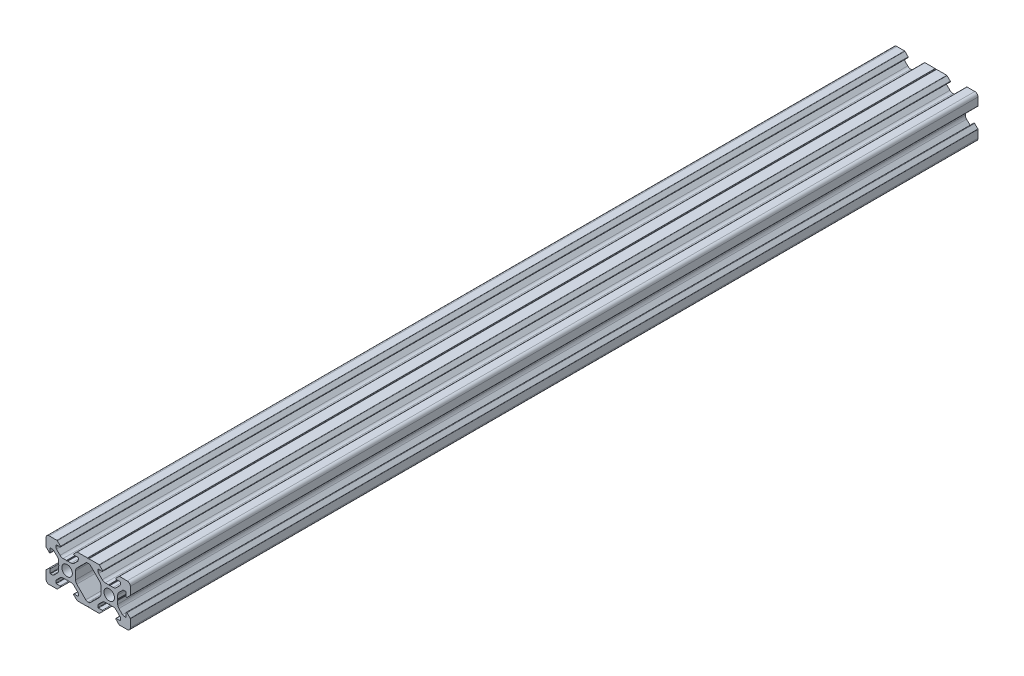
SolidWorks part; units mm, degrees
material "6063-T5"
ref_plane "Спереди" through (0, 0, 0) normal (0, 0, 1) x (1, 0, 0)
ref_plane "Сверху" through (0, 0, 0) normal (0, 1, 0) x (1, 0, 0)
ref_plane "Справа" through (0, 0, 0) normal (1, 0, 0) x (0, 0, -1)
sketch "Model" plane through (0, 0, 0) normal (0, 0, 1) x (1, 0, 0)
  line L0 (-5.4142, 2.9753) -> (-1.1373, 7.2523)
  line L1 (-6, -2.2365) -> (-6, 1.5611)
  line L2 (-5.4142, -3.6507) -> (-1.1373, -7.9276)
  line L3 (-0.1473, -8.3377) -> (0.1473, -8.3377)
  line L4 (5.4142, -3.6507) -> (1.1373, -7.9276)
  line L5 (6, -2.2365) -> (6, 1.5611)
  line L6 (5.4142, 2.9753) -> (1.1373, 7.2523)
  line L7 (-0.1473, 7.6623) -> (0.1473, 7.6623)
  line L8 (0.3757, 9.6623) -> (5.17, 9.6623)
  line L9 (5.3468, 9.5891) -> (6.8468, 8.0891)
  line L10 (6.67, 7.6623) -> (4.9, 7.6623)
  line L11 (4.7, 7.4623) -> (4.7, 6.6493)
  line L12 (4.9929, 5.9422) -> (6.687, 4.2481)
  line L13 (8.1012, 3.6623) -> (9.6623, 3.6623)
  line L14 (9.8185, 3.6075) -> (10, 3.4623)
  line L15 (10.1815, 3.6075) -> (10, 3.4623)
  line L16 (13.313, 4.2481) -> (15.0071, 5.9422)
  line L17 (15.3, 6.6493) -> (15.3, 7.4623)
  line L18 (15.1, 7.6623) -> (13.33, 7.6623)
  line L19 (14.6532, 9.5891) -> (13.1532, 8.0891)
  line L20 (14.83, 9.6623) -> (18.5, 9.6623)
  line L21 (20, 4.4923) -> (20, 8.1623)
  line L22 (19.9268, 4.3155) -> (18.4268, 2.8155)
  line L23 (18, 4.7623) -> (18, 2.9923)
  line L24 (16.987, 4.9623) -> (17.8, 4.9623)
  line L25 (14.5858, 2.9753) -> (16.2799, 4.6694)
  line L26 (14, 0) -> (14, 1.5611)
  line L27 (13.9452, -0.1562) -> (13.8, -0.3377)
  line L28 (13.9452, -0.5192) -> (13.8, -0.3377)
  line L29 (14, -0.6754) -> (14, -2.2365)
  line L30 (14.5858, -3.6507) -> (16.2799, -5.3448)
  line L31 (16.987, -5.6377) -> (17.8, -5.6377)
  line L32 (18, -5.4377) -> (18, -3.6677)
  line L33 (19.9268, -4.9909) -> (18.4268, -3.4909)
  line L34 (20, -5.1677) -> (20, -8.8377)
  line L35 (14.83, -10.3377) -> (18.5, -10.3377)
  line L36 (14.6532, -10.2645) -> (13.1532, -8.7645)
  line L37 (15.1, -8.3377) -> (13.33, -8.3377)
  line L38 (15.3, -7.3247) -> (15.3, -8.1377)
  line L39 (13.313, -4.9235) -> (15.0071, -6.6176)
  line L40 (10.3377, -4.3377) -> (11.8988, -4.3377)
  line L41 (10.1815, -4.2829) -> (10, -4.1377)
  line L42 (9.8185, -4.2829) -> (10, -4.1377)
  line L43 (8.1012, -4.3377) -> (9.6623, -4.3377)
  line L44 (4.9929, -6.6176) -> (6.687, -4.9235)
  line L45 (4.7, -8.1377) -> (4.7, -7.3247)
  line L46 (6.67, -8.3377) -> (4.9, -8.3377)
  line L47 (5.3468, -10.2645) -> (6.8468, -8.7645)
  line L48 (0.3757, -10.3377) -> (5.17, -10.3377)
  line L49 (0, -10.1377) -> (0.237, -10.2957)
  line L50 (0, -10.1377) -> (-0.237, -10.2957)
  line L51 (-0.3757, -10.3377) -> (-5.17, -10.3377)
  line L52 (-5.3468, -10.2645) -> (-6.8468, -8.7645)
  line L53 (-6.67, -8.3377) -> (-4.9, -8.3377)
  line L54 (-4.7, -8.1377) -> (-4.7, -7.3247)
  line L55 (-4.9929, -6.6176) -> (-6.687, -4.9235)
  line L56 (-8.1012, -4.3377) -> (-9.6623, -4.3377)
  line L57 (-9.8185, -4.2829) -> (-10, -4.1377)
  line L58 (-10.1815, -4.2829) -> (-10, -4.1377)
  line L59 (-10.3377, -4.3377) -> (-11.8988, -4.3377)
  line L60 (-13.313, -4.9235) -> (-15.0071, -6.6176)
  line L61 (-15.3, -7.3247) -> (-15.3, -8.1377)
  line L62 (-15.1, -8.3377) -> (-13.33, -8.3377)
  line L63 (-14.6532, -10.2645) -> (-13.1532, -8.7645)
  line L64 (-14.83, -10.3377) -> (-18.5, -10.3377)
  line L65 (-20, -5.1677) -> (-20, -8.8377)
  line L66 (-19.9268, -4.9909) -> (-18.4268, -3.4909)
  line L67 (-18, -5.4377) -> (-18, -3.6677)
  line L68 (-16.987, -5.6377) -> (-17.8, -5.6377)
  line L69 (-14.5858, -3.6507) -> (-16.2799, -5.3448)
  line L70 (-14, -0.6754) -> (-14, -2.2365)
  line L71 (-13.9452, -0.5192) -> (-13.8, -0.3377)
  line L72 (-13.9452, -0.1562) -> (-13.8, -0.3377)
  line L73 (-14, 0) -> (-14, 1.5611)
  line L74 (-14.5858, 2.9753) -> (-16.2799, 4.6694)
  line L75 (-16.987, 4.9623) -> (-17.8, 4.9623)
  line L76 (-18, 4.7623) -> (-18, 2.9923)
  line L77 (-19.9268, 4.3155) -> (-18.4268, 2.8155)
  line L78 (-20, 4.4923) -> (-20, 8.1623)
  line L79 (-14.6532, 9.5891) -> (-13.1532, 8.0891)
  line L80 (-10.1815, 3.6075) -> (-10, 3.4623)
  line L81 (-9.8185, 3.6075) -> (-10, 3.4623)
  line L82 (-8.1012, 3.6623) -> (-9.6623, 3.6623)
  line L83 (-4.9929, 5.9422) -> (-6.687, 4.2481)
  line L84 (-4.7, 7.4623) -> (-4.7, 6.6493)
  line L85 (-6.67, 7.6623) -> (-4.9, 7.6623)
  line L86 (-5.3468, 9.5891) -> (-6.8468, 8.0891)
  line L87 (-0.3757, 9.6623) -> (-5.17, 9.6623)
  line L88 (0, 9.4623) -> (-0.237, 9.6203)
  line L89 (0, 9.4623) -> (0.237, 9.6203)
  line L90 (10.3377, 3.6623) -> (11.8988, 3.6623)
  line L91 (-10.3377, 3.6623) -> (-11.8988, 3.6623)
  line L92 (-13.313, 4.2481) -> (-15.0071, 5.9422)
  line L93 (-15.3, 6.6493) -> (-15.3, 7.4623)
  line L94 (-15.1, 7.6623) -> (-13.33, 7.6623)
  line L95 (-14.83, 9.6623) -> (-18.5, 9.6623)
  circle A0 centre (10, -0.3377) radius 2.5
  arc A1 (-0.1473, 7.6623) -> (-1.1373, 7.2523) centre (-0.1473, 6.2623) ccw
  arc A2 (-5.4142, 2.9753) -> (-6, 1.5611) centre (-4, 1.5611) ccw
  arc A3 (-6, -2.2365) -> (-5.4142, -3.6507) centre (-4, -2.2365) ccw
  arc A4 (-1.1373, -7.9276) -> (-0.1473, -8.3377) centre (-0.1473, -6.9377) ccw
  arc A5 (0.1473, -8.3377) -> (1.1373, -7.9276) centre (0.1473, -6.9377) ccw
  arc A6 (5.4142, -3.6507) -> (6, -2.2365) centre (4, -2.2365) ccw
  arc A7 (6, 1.5611) -> (5.4142, 2.9753) centre (4, 1.5611) ccw
  arc A8 (1.1373, 7.2523) -> (0.1473, 7.6623) centre (0.1473, 6.2623) ccw
  arc A9 (0.3757, 9.6623) -> (0.237, 9.6203) centre (0.3757, 9.4123) ccw
  arc A10 (5.3468, 9.5891) -> (5.17, 9.6623) centre (5.17, 9.4123) ccw
  arc A11 (6.67, 7.6623) -> (6.8468, 8.0891) centre (6.67, 7.9123) ccw
  arc A12 (4.9, 7.6623) -> (4.7, 7.4623) centre (4.9, 7.4623) ccw
  arc A13 (4.7, 6.6493) -> (4.9929, 5.9422) centre (5.7, 6.6493) ccw
  arc A14 (6.687, 4.2481) -> (8.1012, 3.6623) centre (8.1012, 5.6623) ccw
  arc A15 (9.8185, 3.6075) -> (9.6623, 3.6623) centre (9.6623, 3.4123) ccw
  arc A16 (10.3377, 3.6623) -> (10.1815, 3.6075) centre (10.3377, 3.4123) ccw
  arc A17 (11.8988, 3.6623) -> (13.313, 4.2481) centre (11.8988, 5.6623) ccw
  arc A18 (15.0071, 5.9422) -> (15.3, 6.6493) centre (14.3, 6.6493) ccw
  arc A19 (15.3, 7.4623) -> (15.1, 7.6623) centre (15.1, 7.4623) ccw
  arc A20 (13.1532, 8.0891) -> (13.33, 7.6623) centre (13.33, 7.9123) ccw
  arc A21 (14.83, 9.6623) -> (14.6532, 9.5891) centre (14.83, 9.4123) ccw
  arc A22 (20, 8.1623) -> (18.5, 9.6623) centre (18.5, 8.1623) ccw
  arc A23 (19.9268, 4.3155) -> (20, 4.4923) centre (19.75, 4.4923) ccw
  arc A24 (18, 2.9923) -> (18.4268, 2.8155) centre (18.25, 2.9923) ccw
  arc A25 (18, 4.7623) -> (17.8, 4.9623) centre (17.8, 4.7623) ccw
  arc A26 (16.987, 4.9623) -> (16.2799, 4.6694) centre (16.987, 3.9623) ccw
  arc A27 (14.5858, 2.9753) -> (14, 1.5611) centre (16, 1.5611) ccw
  arc A28 (13.9452, -0.1562) -> (14, 0) centre (13.75, 0) ccw
  arc A29 (14, -0.6754) -> (13.9452, -0.5192) centre (13.75, -0.6754) ccw
  arc A30 (14, -2.2365) -> (14.5858, -3.6507) centre (16, -2.2365) ccw
  arc A31 (16.2799, -5.3448) -> (16.987, -5.6377) centre (16.987, -4.6377) ccw
  arc A32 (17.8, -5.6377) -> (18, -5.4377) centre (17.8, -5.4377) ccw
  arc A33 (18.4268, -3.4909) -> (18, -3.6677) centre (18.25, -3.6677) ccw
  arc A34 (20, -5.1677) -> (19.9268, -4.9909) centre (19.75, -5.1677) ccw
  arc A35 (18.5, -10.3377) -> (20, -8.8377) centre (18.5, -8.8377) ccw
  arc A36 (14.6532, -10.2645) -> (14.83, -10.3377) centre (14.83, -10.0877) ccw
  arc A37 (13.33, -8.3377) -> (13.1532, -8.7645) centre (13.33, -8.5877) ccw
  arc A38 (15.1, -8.3377) -> (15.3, -8.1377) centre (15.1, -8.1377) ccw
  arc A39 (15.3, -7.3247) -> (15.0071, -6.6176) centre (14.3, -7.3247) ccw
  arc A40 (13.313, -4.9235) -> (11.8988, -4.3377) centre (11.8988, -6.3377) ccw
  arc A41 (10.1815, -4.2829) -> (10.3377, -4.3377) centre (10.3377, -4.0877) ccw
  arc A42 (9.6623, -4.3377) -> (9.8185, -4.2829) centre (9.6623, -4.0877) ccw
  arc A43 (8.1012, -4.3377) -> (6.687, -4.9235) centre (8.1012, -6.3377) ccw
  arc A44 (4.9929, -6.6176) -> (4.7, -7.3247) centre (5.7, -7.3247) ccw
  arc A45 (4.7, -8.1377) -> (4.9, -8.3377) centre (4.9, -8.1377) ccw
  arc A46 (6.8468, -8.7645) -> (6.67, -8.3377) centre (6.67, -8.5877) ccw
  arc A47 (5.17, -10.3377) -> (5.3468, -10.2645) centre (5.17, -10.0877) ccw
  arc A48 (0.237, -10.2957) -> (0.3757, -10.3377) centre (0.3757, -10.0877) ccw
  arc A49 (-0.3757, -10.3377) -> (-0.237, -10.2957) centre (-0.3757, -10.0877) ccw
  arc A50 (-5.3468, -10.2645) -> (-5.17, -10.3377) centre (-5.17, -10.0877) ccw
  arc A51 (-6.67, -8.3377) -> (-6.8468, -8.7645) centre (-6.67, -8.5877) ccw
  arc A52 (-4.9, -8.3377) -> (-4.7, -8.1377) centre (-4.9, -8.1377) ccw
  arc A53 (-4.7, -7.3247) -> (-4.9929, -6.6176) centre (-5.7, -7.3247) ccw
  arc A54 (-6.687, -4.9235) -> (-8.1012, -4.3377) centre (-8.1012, -6.3377) ccw
  arc A55 (-9.8185, -4.2829) -> (-9.6623, -4.3377) centre (-9.6623, -4.0877) ccw
  arc A56 (-10.3377, -4.3377) -> (-10.1815, -4.2829) centre (-10.3377, -4.0877) ccw
  arc A57 (-11.8988, -4.3377) -> (-13.313, -4.9235) centre (-11.8988, -6.3377) ccw
  arc A58 (-15.0071, -6.6176) -> (-15.3, -7.3247) centre (-14.3, -7.3247) ccw
  arc A59 (-15.3, -8.1377) -> (-15.1, -8.3377) centre (-15.1, -8.1377) ccw
  arc A60 (-13.1532, -8.7645) -> (-13.33, -8.3377) centre (-13.33, -8.5877) ccw
  arc A61 (-14.83, -10.3377) -> (-14.6532, -10.2645) centre (-14.83, -10.0877) ccw
  arc A62 (-20, -8.8377) -> (-18.5, -10.3377) centre (-18.5, -8.8377) ccw
  arc A63 (-19.9268, -4.9909) -> (-20, -5.1677) centre (-19.75, -5.1677) ccw
  arc A64 (-18, -3.6677) -> (-18.4268, -3.4909) centre (-18.25, -3.6677) ccw
  arc A65 (-18, -5.4377) -> (-17.8, -5.6377) centre (-17.8, -5.4377) ccw
  arc A66 (-16.987, -5.6377) -> (-16.2799, -5.3448) centre (-16.987, -4.6377) ccw
  arc A67 (-14.5858, -3.6507) -> (-14, -2.2365) centre (-16, -2.2365) ccw
  arc A68 (-13.9452, -0.5192) -> (-14, -0.6754) centre (-13.75, -0.6754) ccw
  arc A69 (-14, 0) -> (-13.9452, -0.1562) centre (-13.75, 0) ccw
  arc A70 (-14, 1.5611) -> (-14.5858, 2.9753) centre (-16, 1.5611) ccw
  arc A71 (-16.2799, 4.6694) -> (-16.987, 4.9623) centre (-16.987, 3.9623) ccw
  arc A72 (-17.8, 4.9623) -> (-18, 4.7623) centre (-17.8, 4.7623) ccw
  arc A73 (-18.4268, 2.8155) -> (-18, 2.9923) centre (-18.25, 2.9923) ccw
  arc A74 (-20, 4.4923) -> (-19.9268, 4.3155) centre (-19.75, 4.4923) ccw
  arc A75 (-18.5, 9.6623) -> (-20, 8.1623) centre (-18.5, 8.1623) ccw
  arc A76 (-14.6532, 9.5891) -> (-14.83, 9.6623) centre (-14.83, 9.4123) ccw
  arc A77 (-13.33, 7.6623) -> (-13.1532, 8.0891) centre (-13.33, 7.9123) ccw
  arc A78 (-15.1, 7.6623) -> (-15.3, 7.4623) centre (-15.1, 7.4623) ccw
  arc A79 (-15.3, 6.6493) -> (-15.0071, 5.9422) centre (-14.3, 6.6493) ccw
  arc A80 (-13.313, 4.2481) -> (-11.8988, 3.6623) centre (-11.8988, 5.6623) ccw
  arc A81 (-10.1815, 3.6075) -> (-10.3377, 3.6623) centre (-10.3377, 3.4123) ccw
  arc A82 (-9.6623, 3.6623) -> (-9.8185, 3.6075) centre (-9.6623, 3.4123) ccw
  arc A83 (-8.1012, 3.6623) -> (-6.687, 4.2481) centre (-8.1012, 5.6623) ccw
  arc A84 (-4.9929, 5.9422) -> (-4.7, 6.6493) centre (-5.7, 6.6493) ccw
  arc A85 (-4.7, 7.4623) -> (-4.9, 7.6623) centre (-4.9, 7.4623) ccw
  arc A86 (-6.8468, 8.0891) -> (-6.67, 7.6623) centre (-6.67, 7.9123) ccw
  arc A87 (-5.17, 9.6623) -> (-5.3468, 9.5891) centre (-5.17, 9.4123) ccw
  arc A88 (-0.237, 9.6203) -> (-0.3757, 9.6623) centre (-0.3757, 9.4123) ccw
  circle A89 centre (-10, -0.3377) radius 2.5
  dimension "D1" = 20
  dimension "D2" = 40
  dimension "D3" = 20
extrude "Body" add sketch "Model" along normal blind 402
cosmetic thread "Cosmetic Thread1" parameters "D1"=16, "D2"=6
cosmetic thread "Cosmetic Thread2" parameters "D1"=16, "D2"=6
cosmetic thread "Cosmetic Thread3" parameters "D1"=16, "D2"=6
cosmetic thread "Cosmetic Thread4" parameters "D1"=16, "D2"=6
hole_wizard "M6x1.0 Tapped Hole3" positions "Sketch4" profile "Sketch5" tap size "M6x1.0" standard "ANSI Metric"
sketch "Sketch4" plane through (0, 0, 402) normal (0, 0, 1) x (1, 0, 0)
  point P0 (-10, -0.3377)
  point P3 (10, -0.3377)
  point P8 (-10, -0.3377)
  point P10 (10, -0.3377)
  point P16 (10, -0.3377)
  point P18 (-10, -0.3377)
sketch "Sketch5" plane through (-10, -0.3377, 402) normal (1, 0, 0) x (0, -1, 0)
  line L0 (0, 0) -> (0, 15)
  line L1 (0, 15) -> (2.5, 13.4978)
  line L2 (2.5, 13.4978) -> (2.5, 0)
  line L5 (2.5, 0) -> (0, 0)
  line L10 (0, 15) -> (-2.5, 13.4978) construction
  line L11 (0, -6.35) -> (0, 107.95) construction
  dimension "Tap Drill Dia." = 5
  dimension "Tap Drill Depth" = 15
  dimension "Drill Angle" = 118
hole_wizard "M6x1.0 Tapped Hole2" positions "Sketch6" profile "Sketch7" tap size "M6x1.0" standard "ANSI Metric"
sketch "Sketch6" plane through (0, 0, 0) normal (0, 0, -1) x (-1, 0, 0)
  point P0 (-10, -0.3377)
  point P3 (10, -0.3377)
sketch "Sketch7" plane through (10, -0.3377, 0) normal (1, 0, 0) x (0, 1, 0)
  line L0 (0, 0) -> (0, 15)
  line L1 (0, 15) -> (2.5, 13.4978)
  line L2 (2.5, 13.4978) -> (2.5, 0)
  line L5 (2.5, 0) -> (0, 0)
  line L10 (0, 15) -> (-2.5, 13.4978) construction
  line L11 (0, -6.35) -> (0, 107.95) construction
  dimension "Tap Drill Dia." = 5
  dimension "Tap Drill Depth" = 15
  dimension "Drill Angle" = 118
